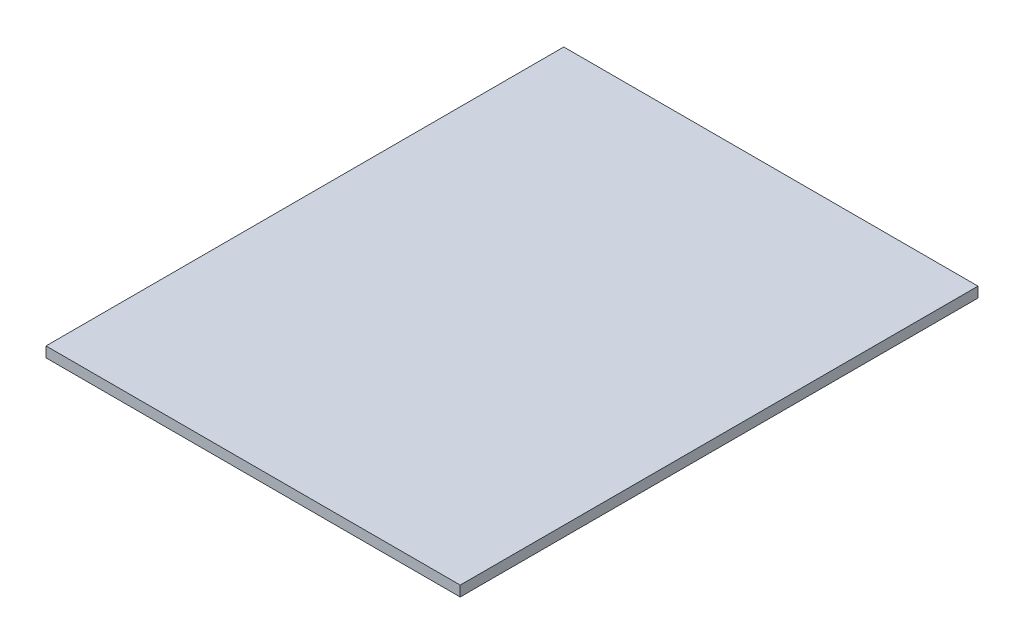
SolidWorks part; units mm, degrees
material "A-Glass Fiber"
ref_plane "Front Plane" through (0, 0, 0) normal (0, 0, 1) x (1, 0, 0)
ref_plane "Top Plane" through (0, 0, 0) normal (0, 1, 0) x (1, 0, 0)
ref_plane "Right Plane" through (0, 0, 0) normal (1, 0, 0) x (0, 0, -1)
sketch "Sketch1" plane through (0, 0, 0) normal (0, 1, 0) x (1, 0, 0)
  line L1 (-60, 75) -> (60, 75)
  line L2 (-60, 75) -> (-60, -75)
  line L3 (-60, -75) -> (60, -75)
  line L4 (60, 75) -> (60, -75)
  line L5 (-60, 75) -> (60, -75) construction
  line L6 (-60, -75) -> (60, 75) construction
  point P0 (0, 0)
  dimension "D1" = 120
  dimension "D2" = 150
extrude "Boss-Extrude1" add sketch "Sketch1" along normal blind 3
sketch "Sketch2" plane through (0, 0, 0) normal (0, -1, 0) x (1, 0, 0)
  line L0 (50, 65) -> (-50, 65)
  line L1 (-50, 65) -> (-50, -65)
  line L2 (-50, -65) -> (50, -65)
  line L3 (50, -65) -> (50, 65)
  line L4 (60, -75) -> (60, 75)
  line L5 (60, 75) -> (-60, 75)
  line L6 (-60, 75) -> (-60, -75)
  line L7 (-60, -75) -> (60, -75)
  line L8 (60, -75) -> (60, 75)
  line L9 (60, 75) -> (-60, 75)
  line L10 (-60, 75) -> (-60, -75)
  line L11 (-60, -75) -> (60, -75)
  dimension "D1" = 0
  dimension "D2" = 10
extrude "Cut-Extrude1" cut sketch "Sketch2" against normal blind 0.18 contours L2 L3 L0 L1
